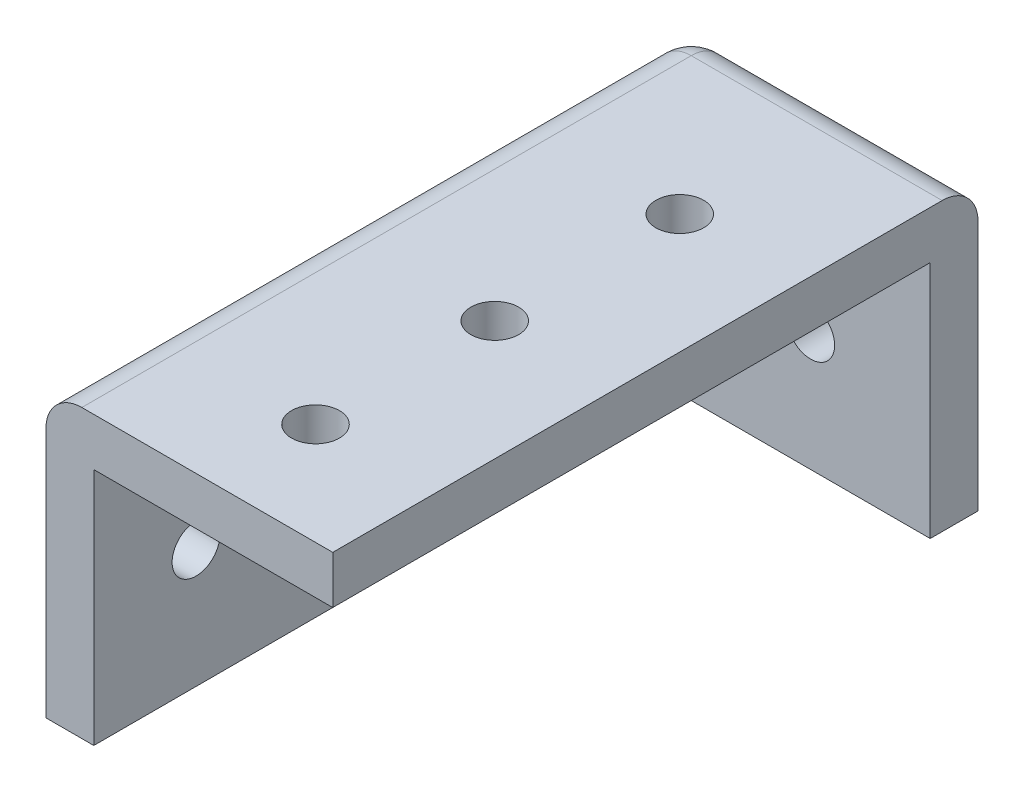
SolidWorks part; units mm, degrees
ref_plane "Front Plane" through (0, 0, 0) normal (0, 0, 1) x (1, 0, 0)
ref_plane "Top Plane" through (0, 0, 0) normal (0, 1, 0) x (1, 0, 0)
ref_plane "Right Plane" through (0, 0, 0) normal (1, 0, 0) x (0, 0, -1)
sketch "Sketch1" plane through (0, 0, 0) normal (0, 0, 1) x (1, 0, 0)
  line L0 (0, 0) -> (0, 24)
  line L1 (0, -55) -> (0, 55) construction
  line L2 (0, 24) -> (24, 24)
  line L3 (24, 24) -> (24, 20)
  line L4 (24, 20) -> (4, 20)
  line L5 (4, 20) -> (4, 0)
  line L6 (55, 0) -> (-55, 0) construction
  line L7 (4, 0) -> (0, 0)
extrude "Boss-Extrude1" add sketch "Sketch1" along normal blind 50
sketch "Sketch2" plane through (0, 0, 0) normal (0, 0, -1) x (-1, 0, 0)
  line L0 (-24, 24) -> (0, 24)
  line L1 (0, 13.2) -> (0, -13.2) construction
  line L2 (-24, 24) -> (0, 24) construction
  line L3 (0, 24) -> (0, 0)
  line L4 (0, 0) -> (-24, 0)
  line L5 (13.2, 0) -> (-13.2, 0) construction
  line L6 (-24, 0) -> (-24, 24)
  dimension "D1" = 24
  dimension "D2" = 24
extrude "Boss-Extrude2" add sketch "Sketch2" along normal blind 4 contours L6 L0 L3 L4
sketch "Sketch3" plane through (0, 0, -4) normal (0, 0, -1) x (-1, 0, 0)
  line L0 (-24, 0) -> (-14, 0) construction
  line L1 (0, 0) -> (-24, 0) construction
  line L2 (-14, 0) -> (-14, 10) construction
  circle A0 centre (-14, 10) radius 2
extrude "Cut-Extrude1" cut sketch "Sketch3" against normal blind 4
sketch "Sketch4" plane through (0, 24, 0) normal (0, 1, 0) x (1, 0, 0)
  line L0 (24, 4) -> (14, 4) construction
  line L1 (24, 4) -> (0, 4) construction
  line L2 (14, 4) -> (14, -10.96) construction
  line L3 (14, -10.96) -> (14, -26.4459) construction
  line L4 (14, -26.4459) -> (14, -41.4459) construction
  circle A0 centre (14, -10.96) radius 2
  circle A1 centre (14, -26.4459) radius 2
  circle A2 centre (14, -41.4459) radius 2
extrude "Cut-Extrude2" cut sketch "Sketch4" against normal blind 4 contours A1 | A0 | A2
ref_plane "Plane1" through (12, 12, 0) normal (-0.7071, -0.7071, 0) x (-0.7071, 0.7071, 0)
mirror "Mirror1" about plane through (12, 12, 0) normal (-0.7071, -0.7071, 0) of "Cut-Extrude2"
fillet "Fillet1" radius 3 3 edges at (0, 12, -4) (12, 24, -4) (0, 24, 23)
